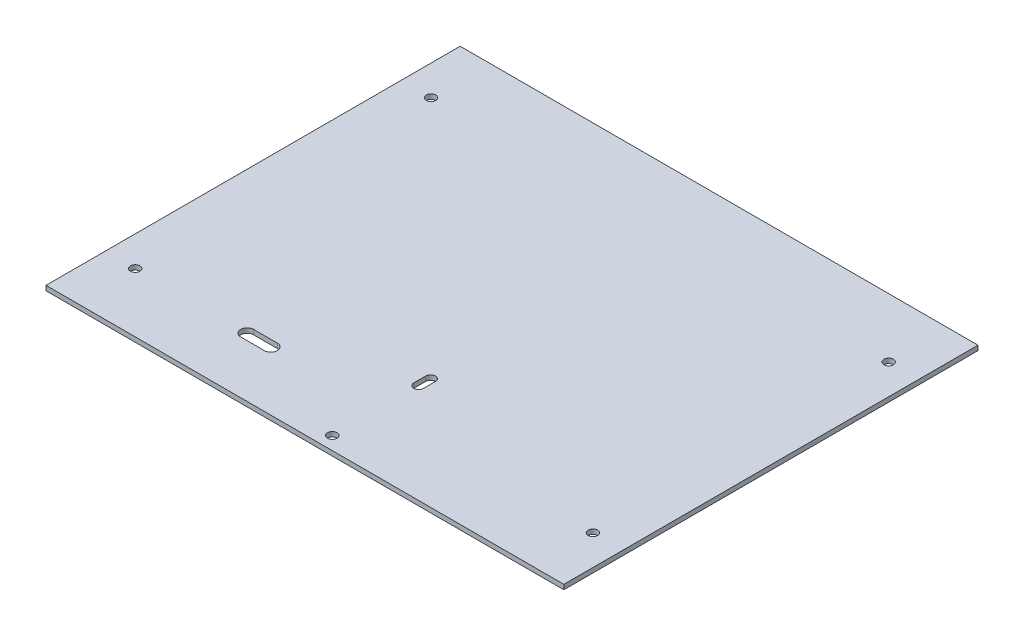
SolidWorks part; units mm, degrees
material "AISI 304"
ref_plane "Front Plane" through (0, 0, 0) normal (0, 0, 1) x (1, 0, 0)
ref_plane "Top Plane" through (0, 0, 0) normal (0, 1, 0) x (1, 0, 0)
ref_plane "Right Plane" through (0, 0, 0) normal (1, 0, 0) x (0, 0, -1)
sketch "Sketch1" plane through (0, 0, 0) normal (0, 1, 0) x (1, 0, 0)
  line L0 (12.044, -90.8875) -> (12.044, -80.8875) construction
  line L1 (218.8, 175) -> (-218.8, 175)
  line L2 (218.8, 175) -> (218.8, -175)
  line L3 (218.8, -175) -> (-218.8, -175)
  line L4 (-218.8, 175) -> (-218.8, -175)
  line L5 (218.8, 175) -> (-218.8, -175) construction
  line L6 (218.8, -175) -> (-218.8, 175) construction
  line L7 (7.979, -90.8875) -> (7.979, -80.8875)
  line L8 (16.109, -90.8875) -> (16.109, -80.8875)
  circle A1 centre (12.044, -163.8875) radius 4.064
  arc A3 (7.979, -90.8875) -> (16.109, -90.8875) centre (12.044, -90.8875) ccw
  arc A4 (16.109, -80.8875) -> (7.979, -80.8875) centre (12.044, -80.8875) ccw
  point P0 (0, 0)
  point P17 (12.044, -85.8875)
  dimension "D3" = 10
  dimension "D4" = 4.065
  dimension "D6" = 78
  dimension "D1" = 437.6
  dimension "D2" = 350
  dimension "D7" = 230.844
extrude "Boss-Extrude1" add sketch "Sketch1" along normal blind 4
sketch "Sketch2" plane through (0, 4, 0) normal (0, 1, 0) x (1, 0, 0)
  line L0 (-218.8, 175) -> (-218.8, -175) construction
  line L1 (218.8, 175) -> (-218.8, 175) construction
  line L2 (-218.8, -175) -> (218.8, -175) construction
  line L4 (0, 175) -> (0, -175) construction
  line L6 (-98.8, -125) -> (-78.8, -125) construction
  line L17 (-98.8, -119.5) -> (-78.8, -119.5)
  line L18 (-98.8, -130.5) -> (-78.8, -130.5)
  circle A0 centre (-193.4, 125) radius 4
  circle A1 centre (-193.4, -125) radius 4
  circle A2 centre (193.4, -125) radius 4
  circle A3 centre (193.4, 125) radius 4
  arc A16 (-98.8, -119.5) -> (-98.8, -130.5) centre (-98.8, -125) ccw
  arc A17 (-78.8, -130.5) -> (-78.8, -119.5) centre (-78.8, -125) ccw
  point P19 (-88.8, -125)
  dimension "D5" = 8
  dimension "D11" = 5.5
  dimension "D1" = 25.4
  dimension "D2" = 25.4
  dimension "D3" = 50
  dimension "D4" = 50
  dimension "D12" = 20
  dimension "D13" = 130
extrude "Cut-Extrude1" cut sketch "Sketch2" against normal through all
